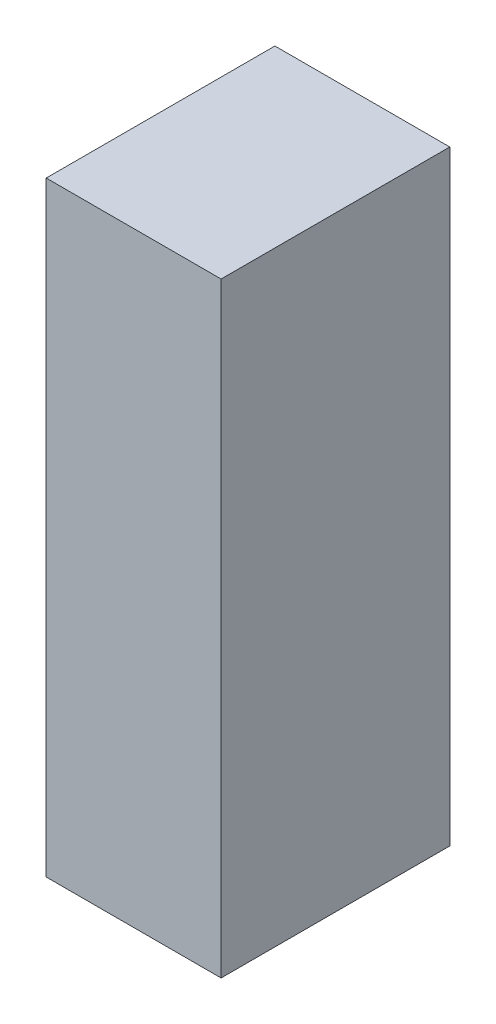
SolidWorks part; units mm, degrees
ref_plane "Front Plane" through (0, 0, 0) normal (0, 0, 1) x (1, 0, 0)
ref_plane "Top Plane" through (0, 0, 0) normal (0, 1, 0) x (1, 0, 0)
ref_plane "Right Plane" through (0, 0, 0) normal (1, 0, 0) x (0, 0, -1)
sketch "Sketch1" plane through (0, 0, 0) normal (0, 1, 0) x (1, 0, 0)
  line L1 (-6.5, 8.5) -> (6.5, 8.5)
  line L2 (-6.5, 8.5) -> (-6.5, -8.5)
  line L3 (-6.5, -8.5) -> (6.5, -8.5)
  line L4 (6.5, 8.5) -> (6.5, -8.5)
  line L5 (-6.5, 8.5) -> (6.5, -8.5) construction
  line L6 (-6.5, -8.5) -> (6.5, 8.5) construction
  point P0 (0, 0)
  dimension "D1" = 17
  dimension "D2" = 13
extrude "Boss-Extrude1" add sketch "Sketch1" along normal blind 45
